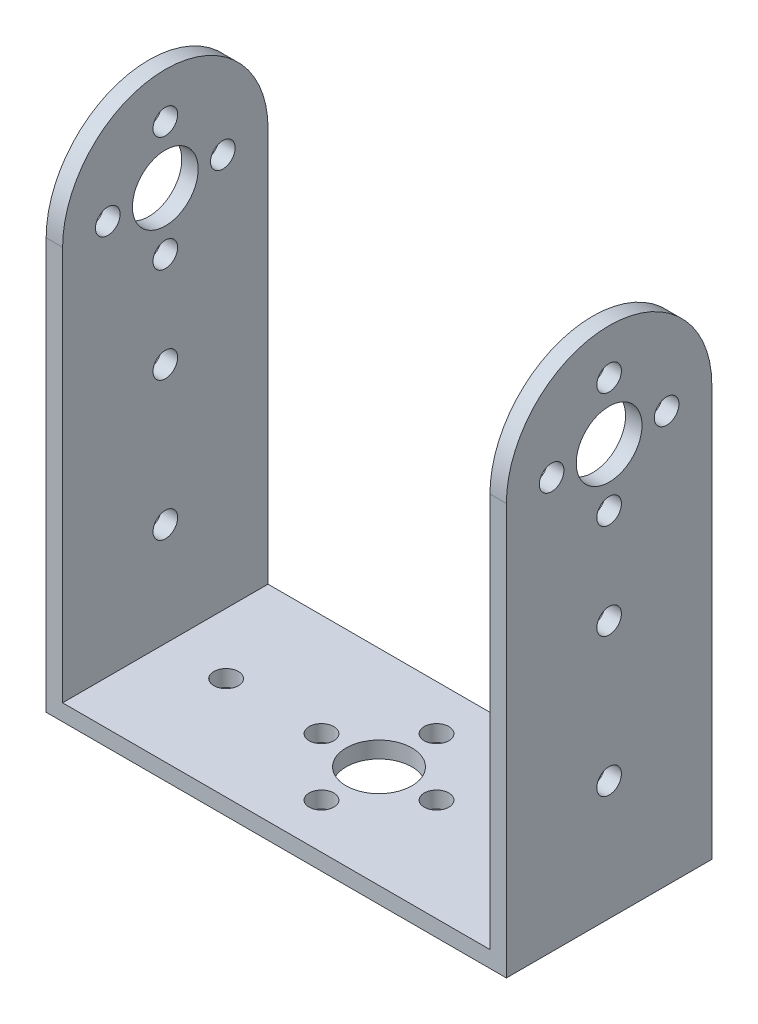
SolidWorks part; units mm, degrees
material "5052-H32"
ref_plane "Front Plane" through (0, 0, 0) normal (0, 0, 1) x (1, 0, 0)
ref_plane "Top Plane" through (0, 0, 0) normal (0, 1, 0) x (1, 0, 0)
ref_plane "Right Plane" through (0, 0, 0) normal (1, 0, 0) x (0, 0, -1)
sketch "Sketch1" plane through (0, 0, 0) normal (0, 1, 0) x (1, 0, 0)
  line L1 (26, -12.5) -> (-26, -12.5)
  line L2 (26, -12.5) -> (26, 12.5)
  line L3 (26, 12.5) -> (-26, 12.5)
  line L4 (-26, -12.5) -> (-26, 12.5)
  line L5 (26, -12.5) -> (-26, 12.5) construction
  line L6 (26, 12.5) -> (-26, -12.5) construction
  circle A0 centre (0, 0) radius 4
  circle A1 centre (18.6, 0) radius 1.5
  circle A2 centre (0, 7) radius 1.5
  circle A3 centre (7, 0) radius 1.5
  circle A4 centre (0, -7) radius 1.5
  circle A5 centre (-7, 0) radius 1.5
  circle A6 centre (-18.6, 0) radius 1.5
  point P0 (0, 0)
  dimension "D3" = 3
  dimension "D4" = 8
  dimension "D5" = 3
  dimension "D6" = 3
  dimension "D7" = 3
  dimension "D8" = 3
  dimension "D9" = 3
  dimension "D1" = 52
  dimension "D2" = 25
  dimension "D10" = 18.6
  dimension "D11" = 18.6
extrude "Boss-Extrude1" add sketch "Sketch1" along normal blind 2
sketch "Sketch3" plane through (26, 0, 0) normal (1, 0, 0) x (0, 0, -1)
  line L0 (-12.5, 0) -> (12.5, 0) construction
  line L1 (-12.5, 0) -> (12.5, 0)
  line L2 (-12.5, 0) -> (-12.5, 50)
  line L4 (12.5, 0) -> (12.5, 50)
  line L5 (-12.5, 2) -> (-12.5, 0) construction
  arc A0 (-12.5, 50) -> (12.5, 50) centre (0, 50) cw
  circle A2 centre (0, 50) radius 4
  circle A3 centre (0, 43) radius 1.5
  circle A4 centre (7, 50) radius 1.5
  circle A5 centre (0, 57) radius 1.5
  circle A6 centre (-7, 50) radius 1.5
  circle A7 centre (0, 31.4) radius 1.5
  circle A8 centre (0, 14.53) radius 1.5
  dimension "D4" = 8
  dimension "D5" = 3
  dimension "D6" = 3
  dimension "D7" = 3
  dimension "D8" = 3
  dimension "D9" = 3
  dimension "D10" = 3
  dimension "D1" = 25
  dimension "D2" = 50
  dimension "D11" = 18.6
  dimension "D12" = 16.87
extrude "Boss-Extrude2" add sketch "Sketch3" along normal blind 2
sketch "Sketch4" plane through (-26, 0, 0) normal (-1, 0, 0) x (0, 0, 1)
  line L1 (-12.5, 0) -> (12.5, 0)
  line L2 (-12.5, 0) -> (-12.5, 50)
  line L4 (12.5, 0) -> (12.5, 50)
  arc A0 (-12.5, 50) -> (12.5, 50) centre (0, 50) cw
  circle A1 centre (0, 50) radius 4
  circle A2 centre (0, 57) radius 1.5
  circle A3 centre (7, 50) radius 1.5
  circle A4 centre (-7, 50) radius 1.5
  circle A5 centre (0, 43) radius 1.5
  circle A6 centre (0, 31.4) radius 1.5
  circle A7 centre (0, 14.53) radius 1.5
extrude "Boss-Extrude3" add sketch "Sketch4" along normal blind 2
